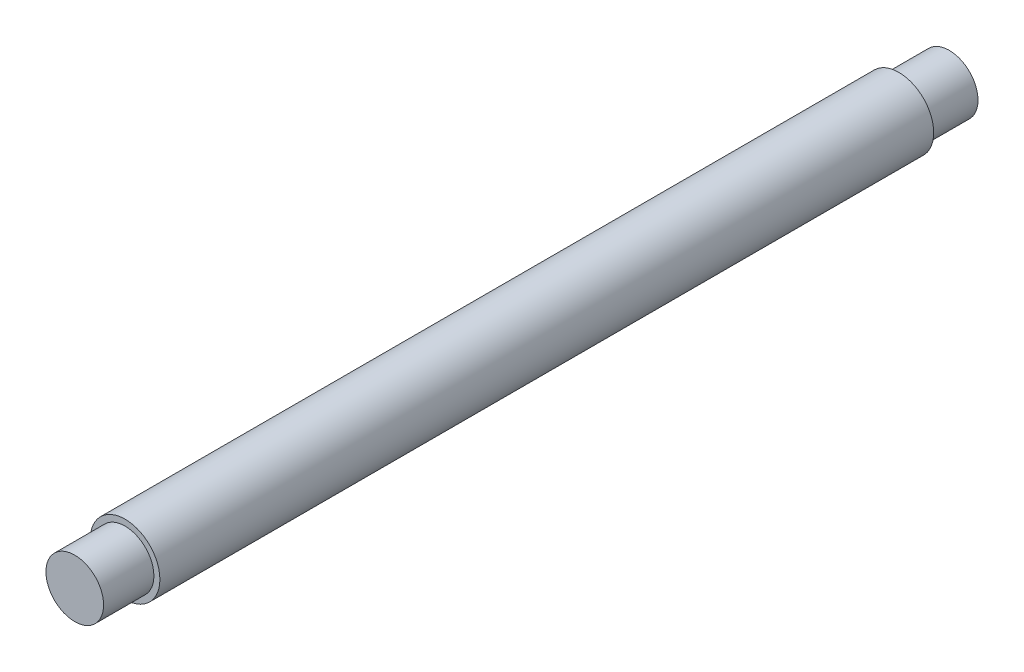
SolidWorks part; units mm, degrees
ref_plane "Ön Düzlem" through (0, 0, 0) normal (0, 0, 1) x (1, 0, 0)
ref_plane "Üst Düzlem" through (0, 0, 0) normal (0, 1, 0) x (1, 0, 0)
ref_plane "Sağ Düzlem" through (0, 0, 0) normal (1, 0, 0) x (0, 0, -1)
sketch "Çizim1" plane through (0, 0, 0) normal (0, 0, 1) x (1, 0, 0)
  circle A0 centre (0, 0) radius 14.9
  dimension "D1" = 29.8
extrude "Yükseklik-Ekstrüzyon1" add sketch "Çizim1" along normal blind 26
sketch "Çizim2" plane through (0, 0, 26) normal (0, 0, 1) x (1, 0, 0)
  circle A0 centre (0, 0) radius 18
  dimension "D1" = 36
extrude "Yükseklik-Ekstrüzyon2" add sketch "Çizim2" along normal blind 400
sketch "Çizim4" plane through (0, 0, 426) normal (0, 0, 1) x (1, 0, 0)
  circle A0 centre (0, 0) radius 14.9
  dimension "D1" = 29.8
extrude "Yükseklik-Ekstrüzyon3" add sketch "Çizim4" along normal blind 26
